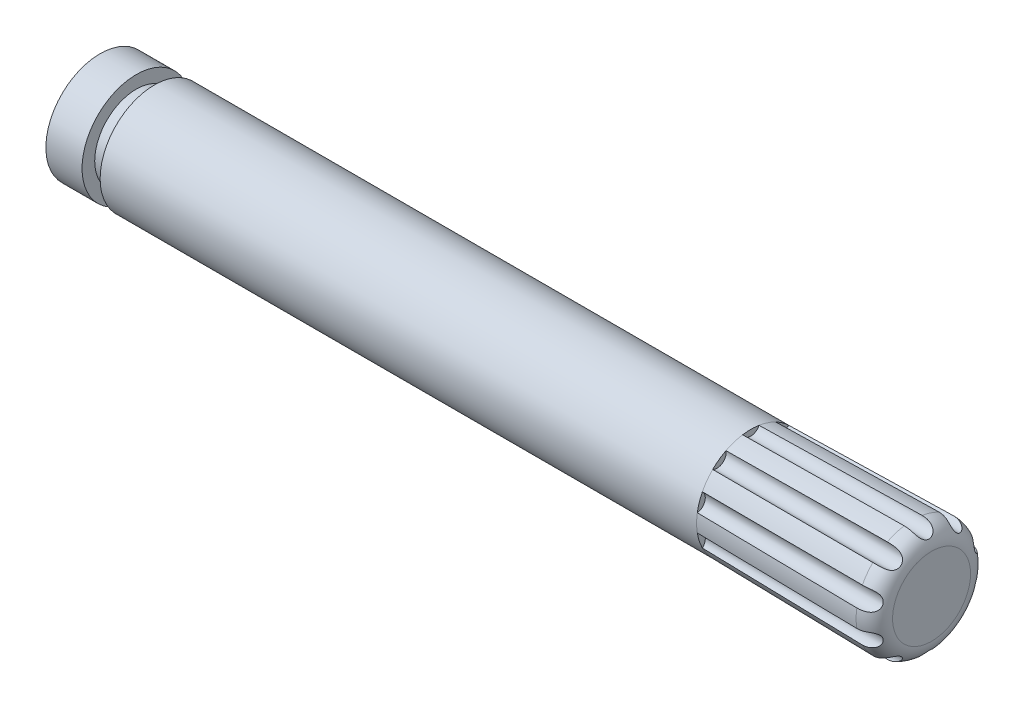
SolidWorks part; units mm, degrees
material "Alloy Steel"
ref_plane "Front" through (0, 0, 0) normal (0, 0, 1) x (1, 0, 0)
ref_plane "Top" through (0, 0, 0) normal (0, 1, 0) x (1, 0, 0)
ref_plane "Right" through (0, 0, 0) normal (1, 0, 0) x (0, 0, -1)
sketch "Sketch1" plane through (0, 0, 0) normal (1, 0, 0) x (0, 0, -1)
  circle A0 centre (0, 0) radius 1.5
  dimension "D1" = 3
extrude "Extrude1" add sketch "Sketch1" against normal blind 18 and the other way blind 5 draft 1
fillet "Fillet1" radius 0.5 1 edges at (5, 0, -1.5873)
sketch "Sketch2" plane through (5, 0, 0) normal (1, 0, 0) x (0, 0, -1)
  circle A0 centre (0, 1.5873) radius 0.25
  circle A1 centre (0, 0) radius 1.5873 construction
  dimension "D1" = 0.5
extrude "Cut-Extrude1" cut sketch "Sketch2" against normal blind 5
pattern_circular "CirPattern1" count 10 over 360 about axis through (0, 0, 0) along (1, 0, 0) of "Cut-Extrude1"
sketch "Sketch3" plane through (0, 0, 0) normal (0, 0, 1) x (1, 0, 0)
  line L0 (-18, 0) -> (-11.7013, 0) construction
  line L1 (-17, 2.0809) -> (-16.5, 2.0809)
  line L2 (-17, 2.0809) -> (-17, 1.15)
  line L3 (-17, 1.15) -> (-16.5, 1.15)
  line L4 (-16.5, 2.0809) -> (-16.5, 1.15)
  line L5 (-18, 1.5) -> (-18, -1.5) construction
  line L6 (5, -1.0785) -> (5, 1.0785) construction
  dimension "D1" = 0.5
  dimension "D2" = 21.5
  dimension "D3" = 2.3
revolve "Cut-Revolve2" cut sketch "Sketch3" angle 360 about L0
